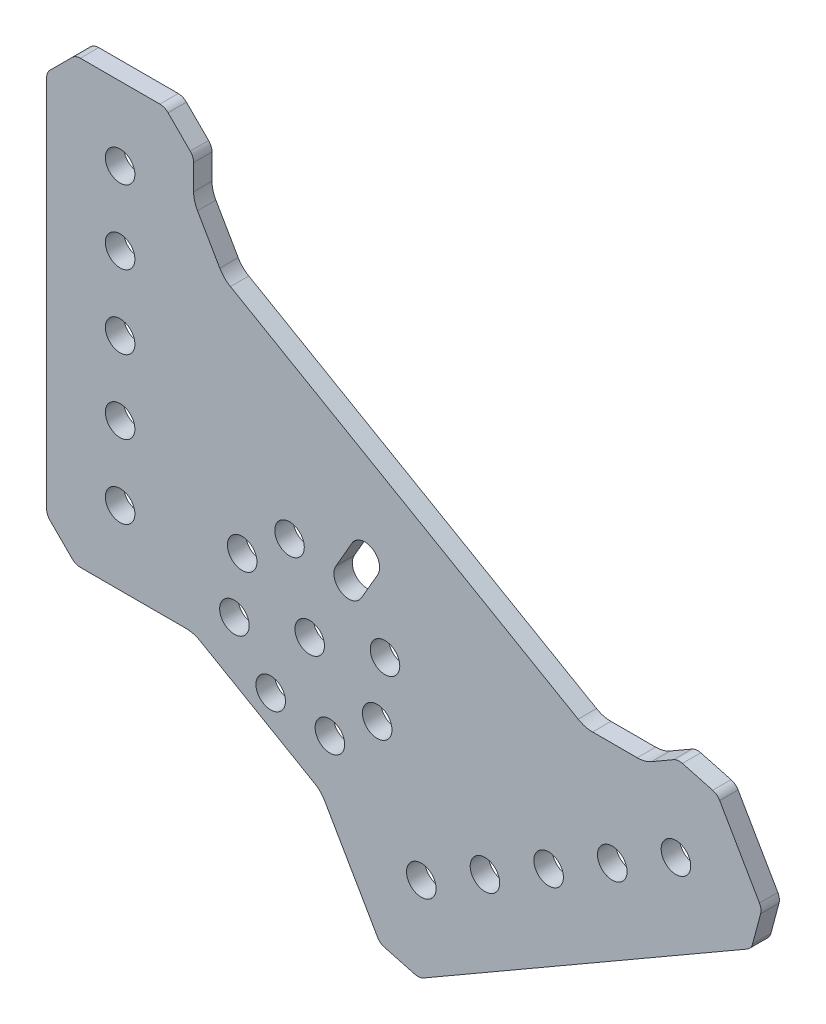
SolidWorks part; units mm, degrees
material "5052-H32"
ref_plane "Front Plane" through (0, 0, 0) normal (0, 0, 1) x (1, 0, 0)
ref_plane "Top Plane" through (0, 0, 0) normal (0, 1, 0) x (1, 0, 0)
ref_plane "Right Plane" through (0, 0, 0) normal (1, 0, 0) x (0, 0, -1)
ref_plane "Plane1" through (0, 0, 0) normal (0, 0, -1) x (-1, 0, 0)
sketch "Sketch1" plane through (0, 0, 0) normal (0, 0, -1) x (-1, 0, 0)
  line L0 (-54.4039, 19.7308) -> (-57.1937, 24.5629)
  line L1 (-52.7723, 27.1156) -> (-49.9825, 22.2835)
  line L2 (-4.4142, 0.5858) -> (-0.5858, 4.4142)
  line L3 (0, 5.8284) -> (0, 70.3716)
  line L4 (-0.5858, 71.7858) -> (-4.4142, 75.6142)
  line L5 (-5.8284, 76.2) -> (-19.5716, 76.2)
  line L6 (-20.9858, 75.6142) -> (-24.8142, 71.7858)
  line L7 (-25.4, 70.3716) -> (-25.4, 65.9985)
  line L8 (-26.0699, 63.4985) -> (-29.9263, 56.819)
  line L9 (-31.7564, 54.9889) -> (-91.8406, 20.2993)
  line L10 (-94.3406, 19.6294) -> (-102.0535, 19.6294)
  line L11 (-104.5535, 20.2993) -> (-108.3406, 22.4858)
  line L12 (-109.8583, 22.6856) -> (-115.088, 21.2843)
  line L13 (-116.3024, 20.3524) -> (-123.174, 8.4505)
  line L14 (-123.3738, 6.9329) -> (-121.9725, 1.7032)
  line L15 (-121.0406, 0.4887) -> (-65.1446, -31.7828)
  line L16 (-63.627, -31.9826) -> (-58.3972, -30.5813)
  line L17 (-57.1828, -29.6495) -> (-48.0669, -13.8603)
  line L18 (-46.2368, -12.0301) -> (-26.5603, -0.6699)
  line L19 (-24.0603, 0) -> (-5.8284, 0)
  circle A0 centre (-33.7923, 16.0766) radius 2.5527
  circle A1 centre (-57.1237, 2.6062) radius 2.5527
  circle A2 centre (-32.4466, 5.855) radius 2.5527
  circle A3 centre (-48.9444, -3.67) radius 2.5527
  circle A4 centre (-12.7, 12.7) radius 2.5527
  circle A5 centre (-12.7, 38.1) radius 2.5527
  circle A6 centre (-12.7, 63.5) radius 2.5527
  circle A7 centre (-64.7456, -17.3485) radius 2.5527
  circle A8 centre (-86.7426, -4.6485) radius 2.5527
  circle A9 centre (-108.7397, 8.0515) radius 2.5527
  circle A10 centre (-12.7, 25.4) radius 2.5527
  circle A11 centre (-12.7, 50.8) radius 2.5527
  circle A12 centre (-75.7441, -10.9985) radius 2.5527
  circle A13 centre (-97.7411, 1.7015) radius 2.5527
  circle A14 centre (-41.9716, 22.3528) radius 2.5527
  circle A15 centre (-58.4694, 12.8278) radius 2.5527
  circle A16 centre (-45.458, 9.3414) radius 2.5527
  circle A17 centre (-38.7228, -2.3243) radius 2.5527
  arc A18 (-57.1937, 24.5629) -> (-52.7723, 27.1156) centre (-54.983, 25.8392) cw
  arc A19 (-49.9825, 22.2835) -> (-54.4039, 19.7308) centre (-52.1932, 21.0071) cw
  arc A20 (-0.5858, 4.4142) -> (0, 5.8284) centre (-2, 5.8284) ccw
  arc A21 (0, 70.3716) -> (-0.5858, 71.7858) centre (-2, 70.3716) ccw
  arc A22 (-4.4142, 75.6142) -> (-5.8284, 76.2) centre (-5.8284, 74.2) ccw
  arc A23 (-19.5716, 76.2) -> (-20.9858, 75.6142) centre (-19.5716, 74.2) ccw
  arc A24 (-24.8142, 71.7858) -> (-25.4, 70.3716) centre (-23.4, 70.3716) ccw
  arc A25 (-25.4, 65.9985) -> (-26.0699, 63.4985) centre (-30.4, 65.9985) cw
  arc A26 (-29.9263, 56.819) -> (-31.7564, 54.9889) centre (-34.2564, 59.319) cw
  arc A27 (-91.8406, 20.2993) -> (-94.3406, 19.6294) centre (-94.3406, 24.6294) cw
  arc A28 (-102.0535, 19.6294) -> (-104.5535, 20.2993) centre (-102.0535, 24.6294) cw
  arc A29 (-108.3406, 22.4858) -> (-109.8583, 22.6856) centre (-109.3406, 20.7537) ccw
  arc A30 (-115.088, 21.2843) -> (-116.3024, 20.3524) centre (-114.5703, 19.3524) ccw
  arc A31 (-123.174, 8.4505) -> (-123.3738, 6.9329) centre (-121.4419, 7.4505) ccw
  arc A32 (-121.9725, 1.7032) -> (-121.0406, 0.4887) centre (-120.0406, 2.2208) ccw
  arc A33 (-65.1446, -31.7828) -> (-63.627, -31.9826) centre (-64.1446, -30.0508) ccw
  arc A34 (-58.3972, -30.5813) -> (-57.1828, -29.6495) centre (-58.9149, -28.6495) ccw
  arc A35 (-48.0669, -13.8603) -> (-46.2368, -12.0301) centre (-43.7368, -16.3603) cw
  arc A36 (-26.5603, -0.6699) -> (-24.0603, 0) centre (-24.0603, -5) cw
  arc A37 (-5.8284, 0) -> (-4.4142, 0.5858) centre (-5.8284, 2) ccw
extrude "Boss-Extrude1" add sketch "Sketch1" against normal blind 3.175
